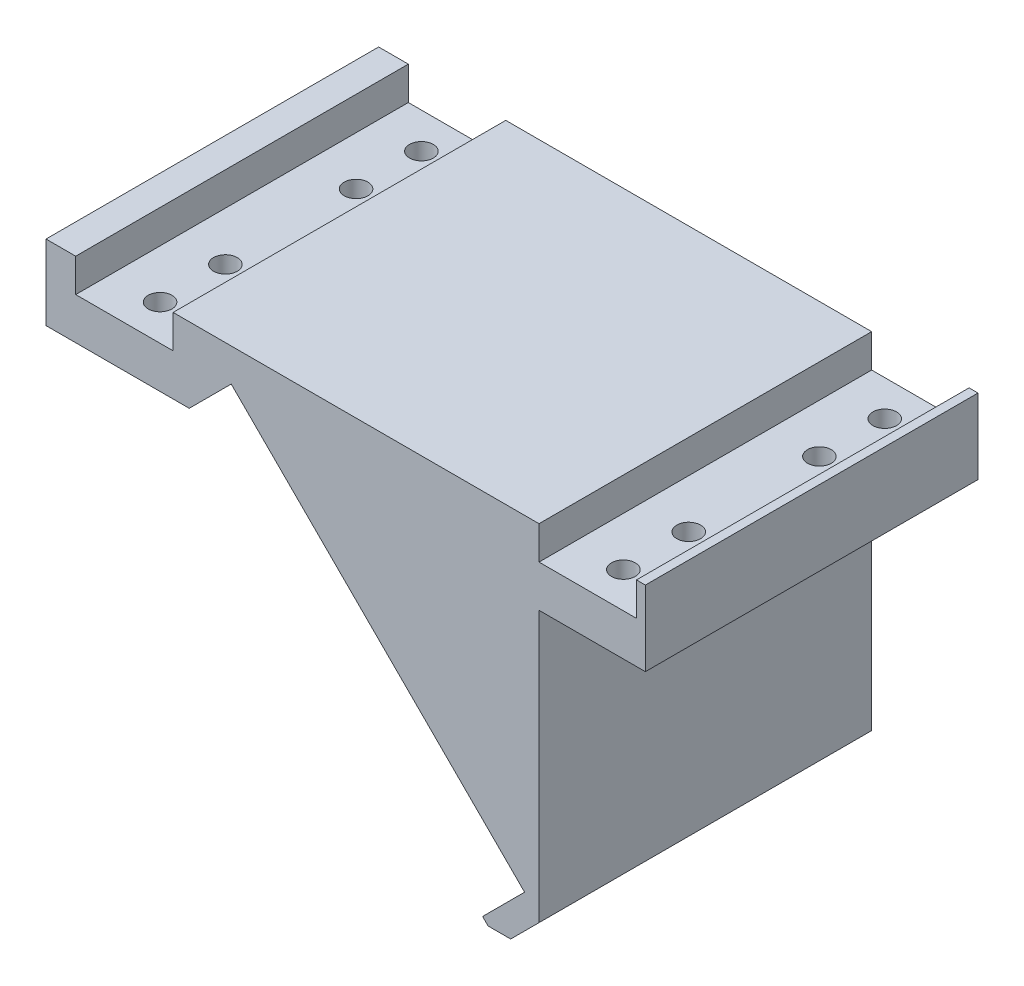
SolidWorks part; units mm, degrees
material "Stainless Steel (ferritic)"
ref_plane "Front" through (0, 0, 0) normal (0, 0, 1) x (1, 0, 0)
ref_plane "Top" through (0, 0, 0) normal (0, 1, 0) x (1, 0, 0)
ref_plane "Right" through (0, 0, 0) normal (1, 0, 0) x (0, 0, -1)
sketch "Sketch1" plane through (0, 0, 0) normal (0, 0, 1) x (1, 0, 0)
  line L0 (13.6979, 25.4191) -> (16.1979, 25.4191)
  line L1 (16.1979, 25.4191) -> (16.1979, 22.6191)
  line L2 (16.1979, 22.6191) -> (24.3979, 22.6191)
  line L3 (24.3979, 22.6191) -> (24.3979, 25.4191)
  line L4 (24.3979, 25.4191) -> (55.1979, 25.4191)
  line L5 (55.1979, 25.4191) -> (55.1979, 22.6191)
  line L6 (55.1979, 22.6191) -> (63.3979, 22.6191)
  line L7 (63.3979, 22.6191) -> (63.3979, 25.4191)
  line L8 (63.3979, 25.4191) -> (64.1479, 25.4191)
  line L9 (64.1479, 25.4191) -> (64.1479, 19.1063)
  line L12 (50.4479, -5.5876) -> (53.9835, -2.0521)
  line L13 (53.9835, -2.0521) -> (29.2895, 22.6418)
  line L14 (29.2895, 22.6418) -> (25.754, 19.1063)
  line L15 (25.754, 19.1063) -> (13.6979, 19.1063)
  line L16 (13.6979, 19.1063) -> (13.6979, 25.4191)
  line L17 (55.1979, 19.1063) -> (64.1479, 19.1063)
  line L18 (55.1979, 19.1063) -> (55.1979, -3.6661)
  line L19 (55.1979, -3.6661) -> (52.8119, -6.0521)
  line L20 (50.9124, -6.0521) -> (50.4479, -5.5876)
  line L21 (50.9124, -6.0521) -> (52.8119, -6.0521)
  point P21 (52.2157, -3.8199)
  dimension "D1" = 30.8
  dimension "D2" = 6.3128
  dimension "D3" = 2.8
  dimension "D4" = 8.2
  dimension "D5" = 0.75
  dimension "D6" = 2.5
  dimension "D7" = 4
  dimension "D8" = 2
  dimension "D9" = 5
extrude "Boss-Extrude1" add sketch "Sketch1" along normal blind 25
sketch "Sketch2" plane through (0, 0, 0) normal (0, 0, -1) x (-1, 0, 0)
  line L0 (-64.1479, 25.4191) -> (-63.3979, 25.4191)
  line L1 (-63.3979, 25.4191) -> (-63.3979, 22.6191)
  line L2 (-63.3979, 22.6191) -> (-55.1979, 22.6191)
  line L3 (-55.1979, 22.6191) -> (-55.1979, 25.4191)
  line L4 (-55.1979, 25.4191) -> (-24.3979, 25.4191)
  line L5 (-24.3979, 25.4191) -> (-24.3979, 22.6191)
  line L6 (-24.3979, 22.6191) -> (-16.1979, 22.6191)
  line L7 (-16.1979, 22.6191) -> (-16.1979, 25.4191)
  line L8 (-16.1979, 25.4191) -> (-13.6979, 25.4191)
  line L9 (-13.6979, 25.4191) -> (-13.6979, 19.1063)
  line L10 (-13.6979, 19.1063) -> (-25.754, 19.1063)
  line L11 (-29.2895, 15.5708) -> (-46.9124, -2.0521)
  line L14 (-52.8119, -6.0521) -> (-55.1979, -3.6661)
  line L15 (-55.1979, -3.6661) -> (-55.1979, 19.1063)
  line L16 (-55.1979, 19.1063) -> (-64.1479, 19.1063)
  line L17 (-64.1479, 19.1063) -> (-64.1479, 25.4191)
  line L18 (-29.2895, 15.5708) -> (-32.8251, 19.1063)
  line L19 (-29.2895, 22.6418) -> (-53.9835, -2.0521) construction
  line L20 (-32.8251, 19.1063) -> (-29.2895, 22.6418)
  line L21 (-29.2895, 22.6418) -> (-25.754, 19.1063)
  line L22 (-50.4479, -5.5876) -> (-53.9835, -2.0521)
  line L23 (-53.9835, -2.0521) -> (-50.4479, 1.4834)
  line L24 (-50.4479, 1.4834) -> (-46.9124, -2.0521)
  line L25 (-50.4479, -5.5876) -> (-50.9124, -6.0521)
  line L26 (-52.8119, -6.0521) -> (-50.9124, -6.0521)
  line L27 (-50.9124, -6.0521) -> (-52.8119, -6.0521) construction
  dimension "D1" = 5
  dimension "D2" = 5
extrude "Boss-Extrude2" add sketch "Sketch2" along normal blind 3
ref_plane "Plane1" through (0, -2.0521, 0) normal (0, -1, 0) x (-1, 0, 0)
hole_wizard "M4x0.7 Tapped Hole1" positions "Sketch7" profile "Sketch8" tap size "M4x0.7" standard "ANSI Metric"
sketch "Sketch7" plane through (0, 0, -3) normal (0, 0, -1) x (-1, 0, 0)
  line L0 (-24.3979, 25.4191) -> (-55.1979, 25.4191) construction
  line L1 (-55.1979, 19.1063) -> (-55.1979, -3.6661) construction
  point P0 (-46.1979, 15.4191)
  dimension "D1" = 10
  dimension "D2" = 9
sketch "Sketch8" plane through (46.1979, 15.4191, -3) normal (1, 0, 0) x (0, 1, 0)
  line L0 (0, 0) -> (0, 14.9914)
  line L1 (0, 14.9914) -> (1.65, 14)
  line L2 (1.65, 14) -> (1.65, 0)
  line L5 (1.65, 0) -> (0, 0)
  line L10 (0, 14.9914) -> (-1.65, 14) construction
  line L11 (0, -6.35) -> (0, 107.95) construction
  dimension "Tap Drill Dia." = 3.3
  dimension "Tap Drill Depth" = 14
  dimension "Drill Angle" = 118
cosmetic thread "Hole Thread2" parameters "D1"=12, "D2"=4
hole_wizard "Ø2.0 (2) Diameter Hole1" positions "Sketch9" profile "Sketch10" hole size "Ø2.0" standard "ANSI Metric" end condition up to next
sketch "Sketch9" plane through (0, 19.1063, 0) normal (0, -1, 0) x (-1, 0, 0)
  line L0 (-64.1479, -25) -> (-64.1479, 3) construction
  line L1 (-55.1979, -25) -> (-64.1479, -25) construction
  line L2 (-64.1479, 3) -> (-55.1979, 3) construction
  point P0 (-59.2979, -22)
  point P1 (-59.2979, -16.5)
  point P5 (-59.2979, -5.5)
  point P7 (-59.2979, 0)
  dimension "D1" = 5.5
  dimension "D2" = 4.85
  dimension "D3" = 5.5
  dimension "D4" = 3
  dimension "D5" = 3
sketch "Sketch10" plane through (59.2979, 19.1063, 22) normal (1, 0, 0) x (0, 0, -1)
  line L0 (0, 0) -> (0, 3.5128)
  line L1 (0, 3.5128) -> (1, 3.5128)
  line L2 (1, 3.5128) -> (1, 0)
  line L5 (1, 0) -> (0, 0)
  line L11 (0, -6.35) -> (0, 107.95) construction
  dimension "Thru Hole Dia." = 2
  dimension "Thru Hole Depth" = 3.5128
hole_wizard "Ø2.0 (2) Diameter Hole2" positions "Sketch11" profile "Sketch12" hole size "Ø2.0" standard "ANSI Metric" end condition up to next
sketch "Sketch11" plane through (0, 19.1063, 0) normal (0, -1, 0) x (-1, 0, 0)
  line L0 (-13.6979, -25) -> (-13.6979, 3) construction
  line L1 (-13.6979, -25) -> (-25.754, -25) construction
  line L2 (-25.754, 3) -> (-13.6979, 3) construction
  point P0 (-20.2979, -22)
  point P2 (-20.2979, -16.5)
  point P4 (-20.2979, -5.5)
  point P6 (-20.2979, 0)
  dimension "D1" = 5.5
  dimension "D2" = 5.5
  dimension "D3" = 6.6
  dimension "D4" = 3
  dimension "D5" = 3
sketch "Sketch12" plane through (20.2979, 19.1063, 22) normal (1, 0, 0) x (0, 0, -1)
  line L0 (0, 0) -> (0, 3.5128)
  line L1 (0, 3.5128) -> (1, 3.5128)
  line L2 (1, 3.5128) -> (1, 0)
  line L5 (1, 0) -> (0, 0)
  line L11 (0, -6.35) -> (0, 107.95) construction
  dimension "Thru Hole Dia." = 2
  dimension "Thru Hole Depth" = 3.5128
hole_wizard "M3x0.5 Tapped Hole1" positions "Sketch13" profile "Sketch14" tap size "M3x0.5" standard "ANSI Metric" end condition up to next
sketch "Sketch13" plane through (29.432, -29.432, 0) normal (0.7071, -0.7071, 0) x (0, 0, -1)
  line L0 (3, 36.4385) -> (3, 33.0642) construction
  line L1 (-25, 33.0642) -> (3, 33.0642) construction
  point P0 (-11, 34.7642)
  dimension "D1" = 14
  dimension "D2" = 1.7
sketch "Sketch14" plane through (54.014, -4.85, 11) normal (0, 0, 1) x (0.7071, 0.7071, 0)
  line L0 (0, 0) -> (0, 2)
  line L1 (0, 2) -> (1.25, 2)
  line L2 (1.25, 2) -> (1.25, 0)
  line L5 (1.25, 0) -> (0, 0)
  line L11 (0, -6.35) -> (0, 107.95) construction
  dimension "Thru Tap Drill Dia." = 2.5
  dimension "Thru Tap Drill Depth" = 2
cosmetic thread "Hole Thread3" parameters "D2"=3
